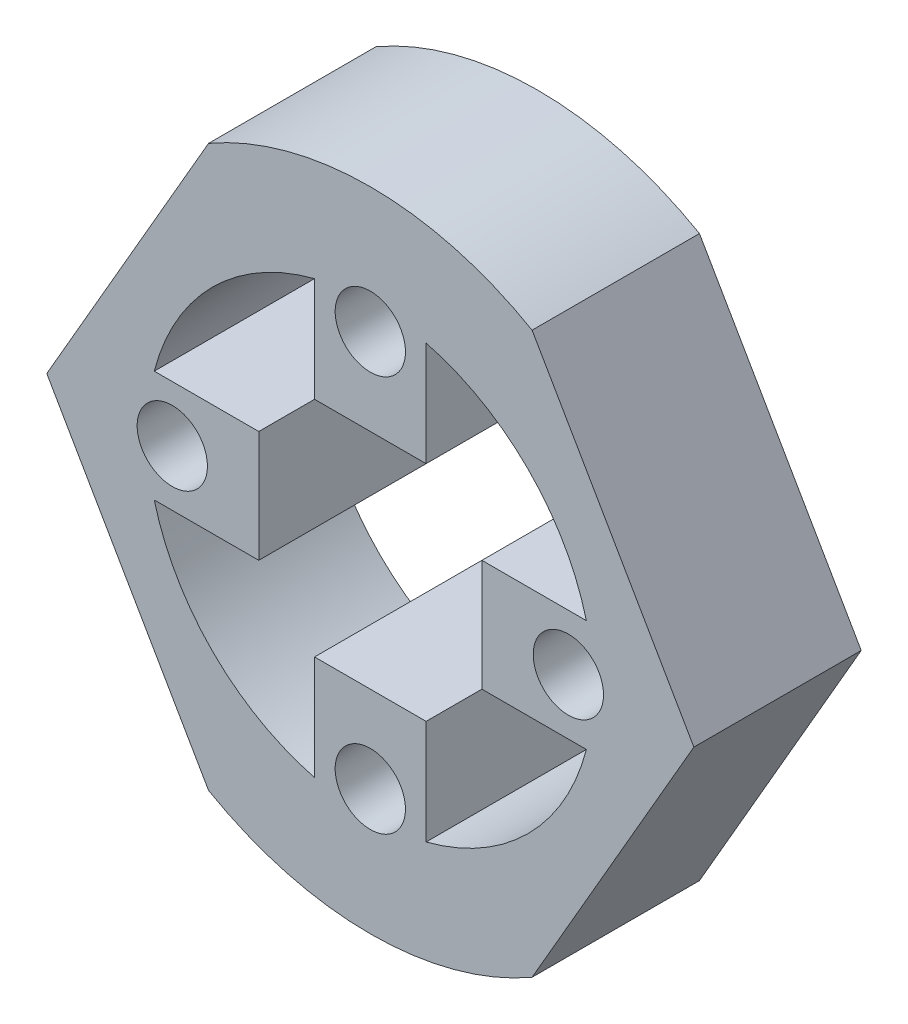
SolidWorks part; units mm, degrees
ref_plane "Front Plane" through (0, 0, 0) normal (0, 0, 1) x (1, 0, 0)
ref_plane "Top Plane" through (0, 0, 0) normal (0, 1, 0) x (1, 0, 0)
ref_plane "Right Plane" through (0, 0, 0) normal (1, 0, 0) x (0, 0, -1)
sketch "Sketch6" plane through (0, 0, 0) normal (0, 0, 1) x (1, 0, 0)
  circle A0 centre (0, 0) radius 20
  circle A1 centre (0, 0) radius 29
  dimension "D1" = 40
  dimension "D2" = 58
extrude "Inner Ring" add sketch "Sketch6" against normal blind 15 separate body
sketch "Sketch7" plane through (0, 0, 0) normal (0, 0, 1) x (1, 0, 0)
  line L2 (-10, 5) -> (-10, -5)
  line L3 (-5, 10) -> (5, 10)
  line L4 (10, 5) -> (10, -5)
  line L5 (-5, -10) -> (5, -10)
  line L14 (-19.3649, 5) -> (-10, 5)
  line L15 (-19.3649, -5) -> (-10, -5)
  line L16 (-5, 19.3649) -> (-5, 10)
  line L17 (5, 19.3649) -> (5, 10)
  line L18 (19.3649, 5) -> (10, 5)
  line L19 (19.3649, -5) -> (10, -5)
  line L20 (5, -19.3649) -> (5, -10)
  line L21 (-5, -19.3649) -> (-5, -10)
  circle A1 centre (0, 0) radius 20
  circle M19 centre (0, 0) radius 20
  dimension "D1" = 20
  dimension "D2" = 20
  dimension "D3" = 10
  dimension "D5" = 10
  dimension "D7" = 10
  dimension "D8" = 10
extrude "Motor Connector Cut" add sketch "Sketch7" against normal blind 15 contours L19 L18 L4 M19 | L17 L16 L3 M19 | L15 L2 L14 M19 | L21 L20 L5 M19
sketch "Sketch9" plane through (0, 0, -15) normal (0, 0, -1) x (-1, 0, 0)
  line L1 (29, 0) -> (14.5, 25.1147)
  line L3 (-14.5, 25.1147) -> (-29, 0)
  line L4 (-29, 0) -> (-14.5, -25.1147)
  line L6 (14.5, -25.1147) -> (29, 0)
  line L7 (14.5, 25.1147) -> (0, 25.1147) [skipped]
  line L8 (0, -25.1147) -> (14.5, -25.1147) [skipped]
  circle A2 centre (0, 0) radius 29
  circle M28 centre (0, 0) radius 29
extrude "Cut-Extrude1" cut sketch "Sketch9" against normal blind 27 and the other way blind 16 contours L1 M28 | L3 M28 | L4 M28 | L6 M28
sketch "Sketch10" plane through (0, 0, -15) normal (0, 0, -1) x (-1, 0, 0)
  circle A3 centre (-17.75, 0) radius 3.15
  circle A4 centre (0, 17.75) radius 3.15
  circle A5 centre (17.75, 0) radius 3.15
  circle A6 centre (0, -17.75) radius 3.15
  dimension "D1" = 6.3
  dimension "D2" = 6.3
  dimension "D4" = 6.3
  dimension "D5" = 6.3
extrude "Cut-Extrude2" cut sketch "Sketch10" against normal blind 70 and the other way blind 55
